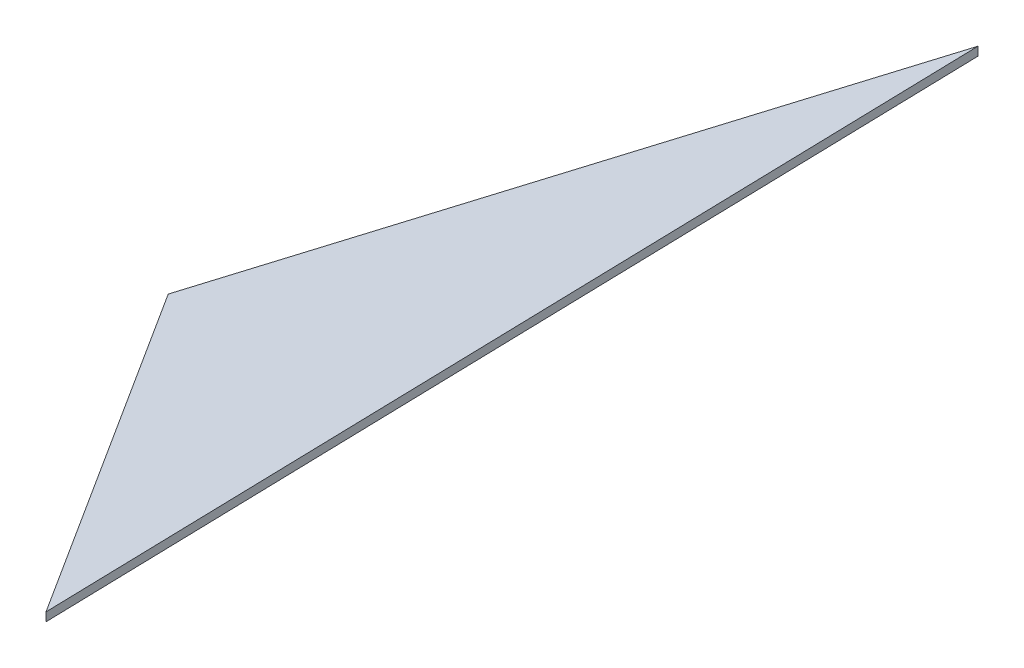
SolidWorks part; units mm, degrees
ref_plane "Plan de face" through (0, 0, 0) normal (0, 0, 1) x (1, 0, 0)
ref_plane "Plan de dessus" through (0, 0, 0) normal (0, 1, 0) x (1, 0, 0)
ref_plane "Plan de droite" through (0, 0, 0) normal (1, 0, 0) x (0, 0, -1)
sketch "Esquisse1" plane through (0, 0, 0) normal (0, 1, 0) x (1, 0, 0)
  line L0 (44.0248, 143.4109) -> (0, 0)
  line L1 (0, 0) -> (49.5561, -77.8448)
  line L2 (49.5561, -77.8448) -> (44.0248, 143.4109)
  point P3 (0, 0)
extrude "Boss.-Extru.1" add sketch "Esquisse1" along normal blind 2
